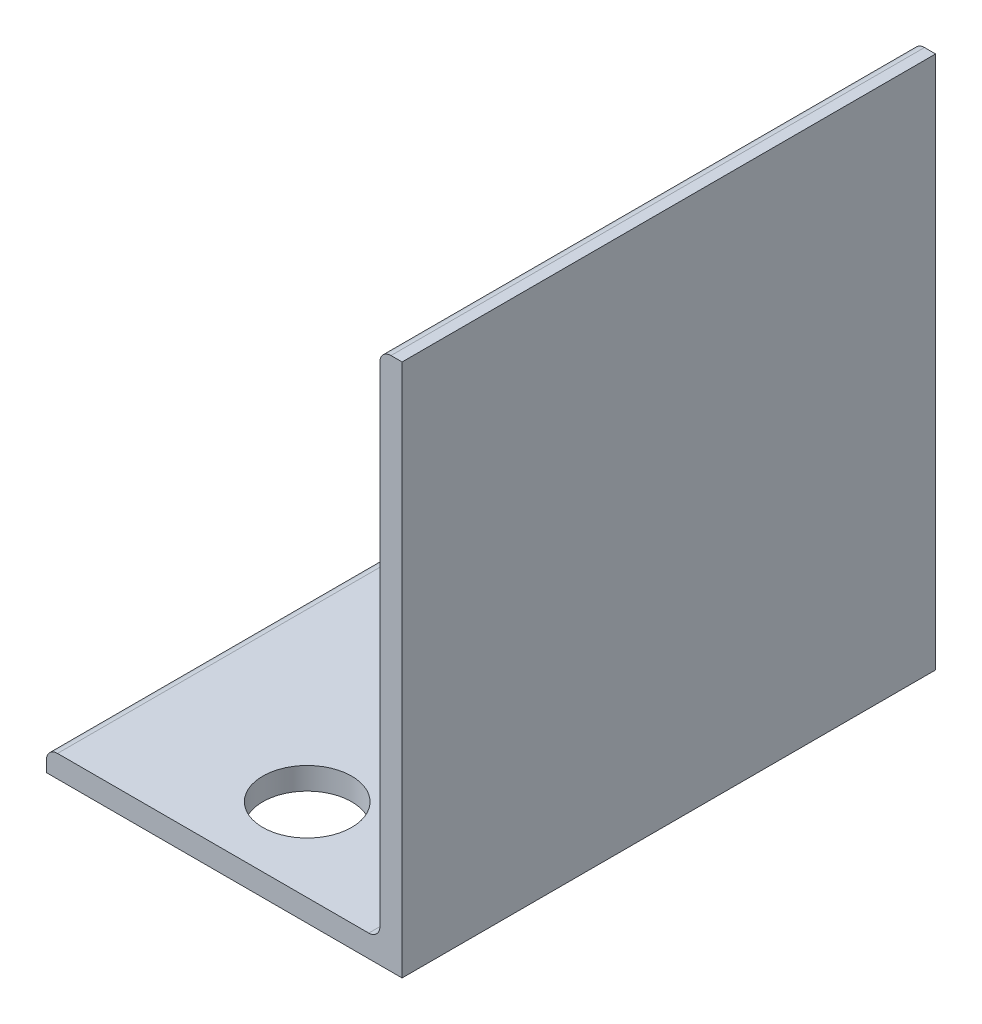
SolidWorks part; units mm, degrees
ref_plane "Front Plane" through (0, 0, 0) normal (0, 0, 1) x (1, 0, 0)
ref_plane "Top Plane" through (0, 0, 0) normal (0, 1, 0) x (1, 0, 0)
ref_plane "Right Plane" through (0, 0, 0) normal (1, 0, 0) x (0, 0, -1)
sketch "Sketch2" plane through (0, 0, 0) normal (0, 0, 1) x (1, 0, 0)
  line L0 (-50.8, 0) -> (50.8, 0)
  line L1 (50.8, 0) -> (50.8, 152.4)
  line L2 (50.8, 152.4) -> (44.45, 152.4) construction
  line L3 (44.45, 149.225) -> (44.45, 9.525)
  line L4 (41.275, 6.35) -> (-47.625, 6.35)
  line L5 (-50.8, 0) -> (-50.8, 6.35) construction
  line L6 (47.625, 152.4) -> (50.8, 152.4)
  line L7 (-50.8, 3.175) -> (-50.8, 0)
  arc A0 (44.45, 149.225) -> (47.625, 152.4) centre (47.625, 149.225) cw
  arc A1 (-50.8, 3.175) -> (-47.625, 6.35) centre (-47.625, 3.175) cw
  arc A2 (44.45, 9.525) -> (41.275, 6.35) centre (41.275, 9.525) cw
  dimension "Vert" = 152.4
  dimension "Horz" = 101.6
  dimension "Thickness" = 6.35
extrude "Boss-Extrude1" add sketch "Sketch2" along normal mid plane 152.4
ref_plane "Contact Plane 1" through (0, 6.35, 0) normal (0, 1, 0) x (1, 0, 0)
ref_plane "Contact Plane 2" through (44.45, 0, 0) normal (-1, 0, 0) x (0, 0, 1)
sketch "Sketch3" plane through (0, 6.35, 0) normal (0, 1, 0) x (1, 0, 0)
  line L0 (0, 0) -> (-25.0703, 0) construction
  circle A0 centre (0, 52.5) radius 12.7
  circle A1 centre (0, -52.5) radius 12.7
  circle A2 centre (0, 0) radius 10
  dimension "D1" = 25.4
  dimension "D2" = 52.5
  dimension "20.0" = 20
extrude "Cut-Extrude1" cut sketch "Sketch3" against normal through all
